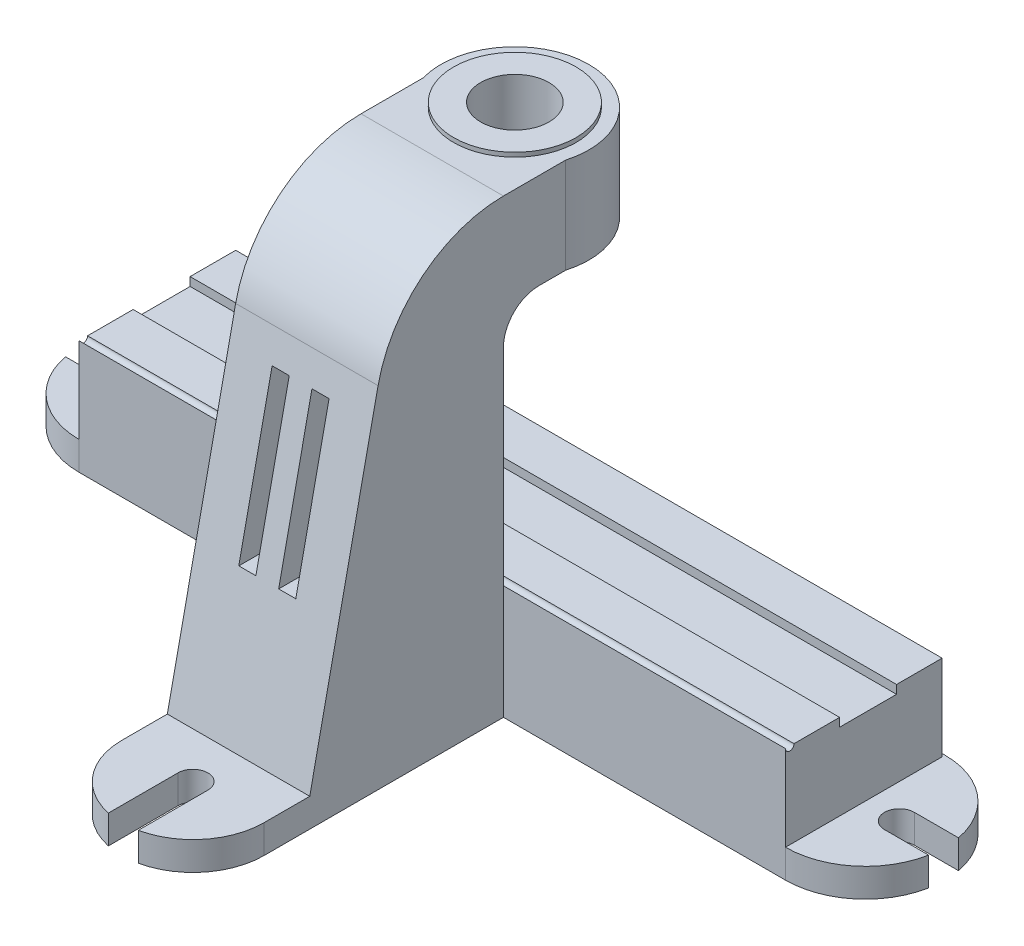
SolidWorks part; units mm, degrees
material "1.0301 (C10)"
ref_plane "Front Plane" through (0, 0, 0) normal (0, 0, 1) x (1, 0, 0)
ref_plane "Top Plane" through (0, 0, 0) normal (0, 1, 0) x (1, 0, 0)
ref_plane "Right Plane" through (0, 0, 0) normal (1, 0, 0) x (0, 0, -1)
sketch "Sketch1" plane through (0, 0, 0) normal (1, 0, 0) x (0, 0, -1)
  line L0 (0, 359.0062) -> (0, -359.0062) construction
  line L1 (-226, 156.061) -> (-226, -77.5773) construction
  line L2 (-226, 0) -> (54, 0)
  line L3 (54, 0) -> (54, 20)
  line L4 (54, 20) -> (52, 20)
  line L5 (52, 20) -> (52, 80)
  line L6 (52, 80) -> (20, 80)
  line L7 (20, 80) -> (20, 74)
  line L8 (20, 74) -> (-20, 74)
  line L9 (-20, 74) -> (-20, 80)
  line L10 (-20, 80) -> (-58, 80)
  line L11 (-58, 80) -> (-58, 250)
  line L12 (-58, 250) -> (0, 250)
  line L14 (0, 317) -> (-58, 317)
  line L15 (-146.0341, 245.7084) -> (-194, 20)
  line L16 (-194, 20) -> (-226, 20)
  line L17 (-226, 20) -> (-226, 0)
  line L18 (0, 317) -> (0, 250)
  arc A0 (-58, 317) -> (-146.0341, 245.7084) centre (-58, 227) ccw
  point P4 (0, 0)
  point P18 (54, 10)
  dimension "D12" = 90
  dimension "D1" = 226
  dimension "D2" = 280
  dimension "D3" = 20
  dimension "D4" = 20
  dimension "D5" = 6
  dimension "D6" = 112
  dimension "D7" = 2
  dimension "D8" = 20
  dimension "D9" = 80
  dimension "D10" = 67
  dimension "D11" = 317
  dimension "D13" = 32
extrude "Boss-Extrude1" add sketch "Sketch1" along normal mid plane 100
sketch "Sketch2" plane through (0, 317, 0) normal (0, 1, 0) x (1, 0, 0)
  line L0 (50, 52) -> (-50, 52) construction
  circle A0 centre (0, 0) radius 52
extrude "Boss-Extrude2" add sketch "Sketch2" against normal up to surface (67 mm away) up to face at (0, 250, 29)
sketch "Sketch3" plane through (0, 317, 0) normal (0, 1, 0) x (1, 0, 0)
  circle A0 centre (0, 0) radius 43
  dimension "D1" = 86
extrude "Boss-Extrude3" add sketch "Sketch3" along normal blind 3
sketch "Sketch4" plane through (0, 320, 0) normal (0, 1, 0) x (1, 0, 0)
  circle A0 centre (0, 0) radius 24
  dimension "D1" = 48
extrude "Cut-Extrude1" cut sketch "Sketch4" against normal up to next
sketch "Sketch5" plane through (0, 250, 0) normal (0, -1, 0) x (1, 0, 0)
  circle A0 centre (0, 0) radius 33
  dimension "D1" = 66
extrude "Cut-Extrude2" cut sketch "Sketch5" against normal blind 4
sketch "Sketch6" plane through (0, 0, 0) normal (1, 0, 0) x (0, 0, -1)
  line L1 (-20, 80) -> (-58, 80) construction
  line L2 (-20, 74) -> (-20, 80) construction
  line L3 (20, 74) -> (-20, 74) construction
  line L4 (20, 80) -> (20, 74) construction
  line L5 (52, 80) -> (20, 80) construction
  line L6 (54, 20) -> (52, 20) construction
  line L7 (54, 0) -> (54, 20) construction
  line L8 (52, 20) -> (52, 80) construction
  line L9 (-58, 80) -> (-58, 0)
  line L10 (-20, 80) -> (-58, 80)
  line L11 (-20, 74) -> (-20, 80)
  line L12 (20, 74) -> (-20, 74)
  line L13 (20, 80) -> (20, 74)
  line L14 (52, 80) -> (20, 80)
  line L15 (54, 20) -> (52, 20)
  line L16 (54, 0) -> (54, 20)
  line L17 (52, 20) -> (52, 80)
  line L18 (-226, 0) -> (54, 0) construction
  line L19 (-58, 0) -> (54, 0)
extrude "Boss-Extrude4" add sketch "Sketch6" along normal mid plane 496
sketch "Sketch7" plane through (0, 0, 0) normal (1, 0, 0) x (0, 0, -1)
  line L0 (-20, 80) -> (-58, 80) construction
  circle A0 centre (-55, 80) radius 3
  dimension "D1" = 6
extrude "Cut-Extrude3" cut sketch "Sketch7" against normal mid plane 496
sketch "Sketch8" plane through (0, 0, 0) normal (0, -1, 0) x (1, 0, 0)
  line L0 (-248, 58) -> (-248, -54) construction
  line L1 (-50, 58) -> (-248, 58) construction
  line L2 (-272, 12.5) -> (-303.0068, 12.5)
  line L3 (-272, -8.5) -> (-303.0068, -8.5)
  line L4 (0, 344.9973) -> (0, -344.9973) construction
  line L5 (272, -8.5) -> (303.0068, -8.5)
  line L6 (272, 12.5) -> (303.0068, 12.5)
  arc A0 (-303.0068, -8.5) -> (-303.0068, 12.5) centre (-248, 2) ccw
  arc A1 (-272, -8.5) -> (-272, 12.5) centre (-272, 2) ccw
  arc A2 (272, -8.5) -> (272, 12.5) centre (272, 2) cw
  arc A3 (303.0068, -8.5) -> (303.0068, 12.5) centre (248, 2) cw
  point P15 (0, 0)
  dimension "D1" = 21
  dimension "D2" = 24
extrude "Boss-Extrude5" add sketch "Sketch8" against normal blind 20
sketch "Sketch9" plane through (0, 20, 0) normal (0, 1, 0) x (1, 0, 0)
  line L0 (50, -226) -> (-50, -226) construction
  circle A0 centre (0, -226) radius 50
extrude "Boss-Extrude6" add sketch "Sketch9" against normal up to surface (20 mm away) up to face at (0, 0, 37)
sketch "Sketch10" plane through (0, 20, 0) normal (0, 1, 0) x (1, 0, 0)
  line L0 (10.5, -226) -> (10.5, -291)
  line L1 (-10.5, -226) -> (-10.5, -291)
  circle A0 centre (0, -226) radius 10.5
  arc A1 (-50, -226) -> (50, -226) centre (0, -226) ccw construction
  arc A2 (10.5, -291) -> (-10.5, -291) centre (0, -291) cw
  arc M4 (-50, -226) -> (50, -226) centre (0, -226) ccw
  dimension "D1" = 21
  dimension "D2" = 65
extrude "Cut-Extrude4" cut sketch "Sketch10" against normal up to next contours A0 | A0 L1 L0 M4 | A2 L0 L1 M4
fillet "Fillet1" radius 25 1 edges at (0, 250, 58)
sketch "Sketch11" plane through (0, 0, 0) normal (1, 0, 0) x (0, 0, -1)
  line L2 (-130.3836, 242.3824) -> (-178.3495, 16.6741)
  line L3 (-130.3836, 242.3824) -> (-181.893, 0)
  line L24 (-33, 266) -> (-33, 301)
  line L25 (-74, 225) -> (-74, 80)
  line L26 (-74, 225) -> (-74, 64)
  line L27 (-33, 301) -> (-58, 301)
  line L28 (-226, 0) -> (-58, 0) construction
  line L29 (-74, 64) -> (0, 64)
  line L30 (0, 64) -> (0, 0)
  line L31 (-20, 80) -> (-52, 80) construction
  line L32 (-181.893, 0) -> (0, 0)
  arc A3 (-58, 301) -> (-130.3836, 242.3824) centre (-58, 227) ccw
  arc A4 (-58, 301) -> (-130.3836, 242.3824) centre (-58, 227) ccw
  arc A25 (-33, 266) -> (-74, 225) centre (-33, 225) ccw
  arc A26 (-33, 266) -> (-74, 225) centre (-33, 225) ccw
  dimension "D3" = 16
  dimension "D1" = 16
  dimension "D2" = 16
extrude "Cut-Extrude5" cut sketch "Sketch11" against normal mid plane 68
ref_plane "Plane1" through (-10.5, 20, 226) normal (0, 0, 1) x (1, 0, 0)
sketch "Sketch12" plane through (0, 0, 0) normal (1, 0, 0) x (0, 0, -1)
  line L0 (-42, 64) -> (36, 64)
  line L2 (36, 64) -> (36, 0)
  line L3 (8.5, 0) -> (54, 0) construction
  line L4 (36, 0) -> (-42, 0)
  line L5 (-42, 0) -> (-42, 64)
  line L6 (-20, 80) -> (-52, 80) construction
  line L7 (52, 20) -> (52, 80) construction
  line L8 (-58, 80) -> (-58, 225) construction
  dimension "D1" = 16
  dimension "D2" = 16
  dimension "D3" = 16
extrude "Cut-Extrude6" cut sketch "Sketch12" against normal mid plane 480
sketch "Sketch13" plane through (0, 0, 58) normal (0, 0, -1) x (-1, 0, 0)
  line L0 (0, 0) -> (0, 356.0111) construction
  line L1 (8, 225) -> (20, 225)
  line L2 (8, 225) -> (8, 115)
  line L3 (8, 115) -> (20, 115)
  line L4 (20, 225) -> (20, 115)
  line L6 (50, 225) -> (-50, 225) construction
  line L7 (-8, 115) -> (-20, 115)
  line L8 (-8, 225) -> (-8, 115)
  line L9 (-8, 225) -> (-20, 225)
  line L10 (-20, 225) -> (-20, 115)
  dimension "D1" = 110
  dimension "D2" = 12
  dimension "D3" = 8
extrude "Cut-Extrude7" cut sketch "Sketch13" against normal mid plane 480
